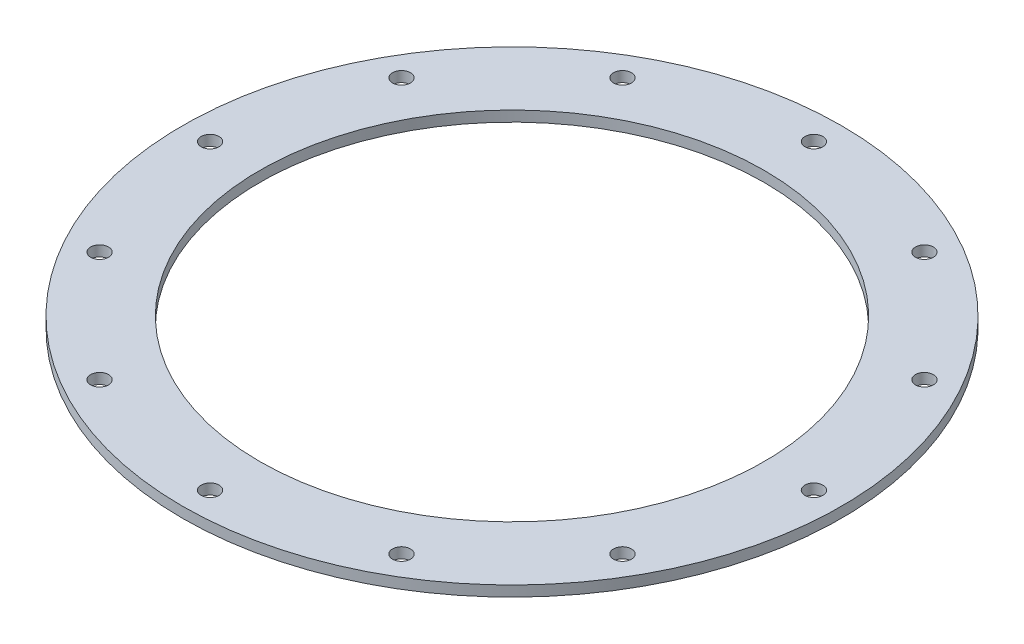
SolidWorks part; units mm, degrees
material "PTFE (general)"
ref_plane "Front Plane" through (0, 0, 0) normal (0, 0, 1) x (1, 0, 0)
ref_plane "Top Plane" through (0, 0, 0) normal (0, 1, 0) x (1, 0, 0)
ref_plane "Right Plane" through (0, 0, 0) normal (1, 0, 0) x (0, 0, -1)
ref_axis "Axis1" through (0, 55, 0) along (0, -1, 0)
sketch "Sketch1" plane through (0, 0, 0) normal (0, 0, 1) x (1, 0, 0)
  line L0 (-38.1, 0) -> (0, 0) construction
  line L1 (-38.1, 0) -> (-49.784, 0)
  line L2 (-38.1, 0) -> (-38.1, 1.5875)
  line L3 (-38.1, 1.5875) -> (-49.784, 1.5875)
  line L4 (-49.784, 0) -> (-49.784, 1.5875)
  line L7 (0, 1.5875) -> (-38.1, 1.5875) construction
  point P12 (-49.784, 0)
  point P18 (-38.1, 1.5875)
  dimension "D1" = 11.684
revolve "Main" add sketch "Sketch1" angle 360 about axis through (0, 55, 0) along (0, -1, 0)
sketch "Hole Location" plane through (0, 0, 0) normal (0, 1, 0) x (1, 0, 0)
  line L0 (0, 0) -> (-45.6057, 0) construction
  circle A0 centre (0, 0) radius 45.6057 construction
  dimension "D1" = 91.2114
hole_wizard "#36 (0.1065) Diameter Hole1" positions "Sketch3" profile "Sketch5" hole size "#36" standard "ANSI Inch" end condition through all
sketch "Sketch3" plane through (0, 0, 0) normal (0, -1, 0) x (-1, 0, 0)
  point P0 (45.6057, 0)
sketch "Sketch5" plane through (-45.6057, 0, 0) normal (1, 0, 0) x (0, 0, -1)
  line L0 (0, 0) -> (0, 1.5875)
  line L1 (0, 1.5875) -> (1.3525, 1.5875)
  line L2 (1.3525, 1.5875) -> (1.3525, 0)
  line L5 (1.3525, 0) -> (0, 0)
  line L11 (0, -6.35) -> (0, 107.95) construction
  dimension "Thru Hole Dia." = 2.7051
  dimension "Thru Hole Depth" = 1.5875
pattern_circular "Screw Passthroughs" count 12 over 360 about axis through (0, 0, 0) along (0, 1, 0) of "#36 (0.1065) Diameter Hole1"
equation "\"D1@Hole Location\"=\"TANK DIAMETER@Cryo Tank.Assembly\"+\"GASKET SEAT THICKNESS@Cryo Tank.Assembly\"+\"LINER THICKNESS@Cryo Tank.Assembly\"+\"SHRINK FIT DELTA@Cryo Tank.Assembly\""
equation "\"D1@Sketch1\"=\"GASKET SEAT THICKNESS@Cryo Tank.Assembly\""
